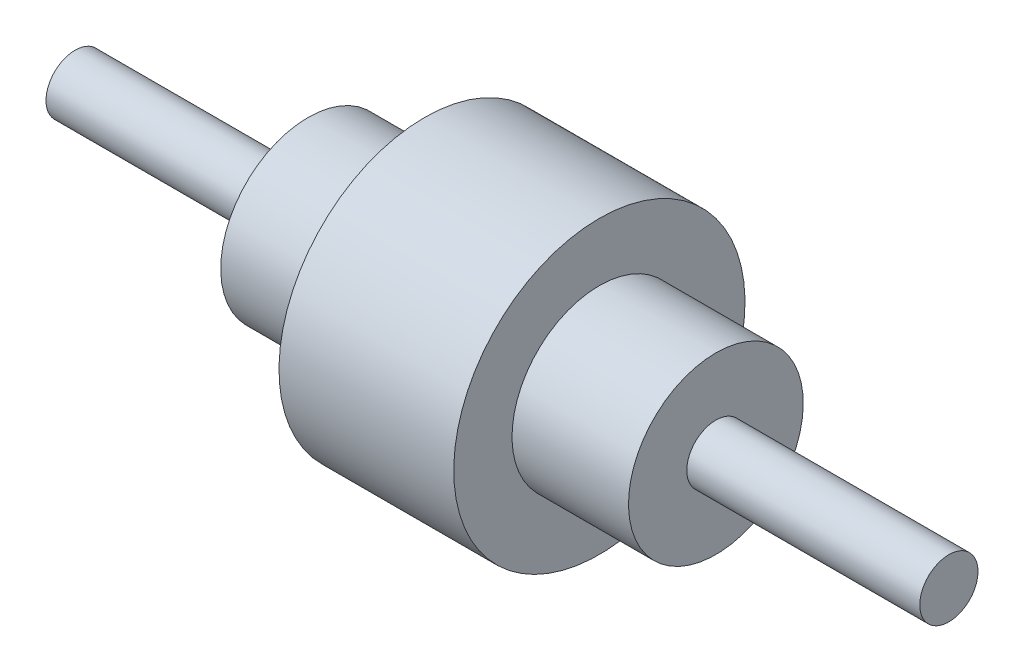
SolidWorks part; units mm, degrees
ref_plane "Front Plane" through (0, 0, 0) normal (0, 0, 1) x (1, 0, 0)
ref_plane "Top Plane" through (0, 0, 0) normal (0, 1, 0) x (1, 0, 0)
ref_plane "Right Plane" through (0, 0, 0) normal (1, 0, 0) x (0, 0, -1)
sketch "Sketch1" plane through (0, 0, 0) normal (0, 0, 1) x (1, 0, 0)
  line L0 (0, 0) -> (-8331.9087, 0) construction
  line L1 (-7620, 0) -> (-7620, -254)
  line L2 (-7620, -254) -> (-5588, -254)
  line L3 (-5588, -254) -> (-5588, -762)
  line L4 (-5588, -762) -> (-4572, -762)
  line L5 (-4572, -762) -> (-4572, -1270)
  line L6 (-4572, -1270) -> (-3048, -1270)
  line L7 (-7620, 0) -> (0, 0)
  line L8 (-3048, -762) -> (-3048, -1270)
  line L9 (-2032, -762) -> (-3048, -762)
  line L10 (-2032, -254) -> (-2032, -762)
  line L11 (0, 0) -> (0, -254)
  line L12 (0, -254) -> (-2032, -254)
  dimension "D1" = 7620
  dimension "D2" = 508
  dimension "D3" = 1524
  dimension "D4" = 2540
  dimension "D5" = 2032
  dimension "D6" = 1016
revolve "Revolve1" add sketch "Sketch1" angle 360 about L0
